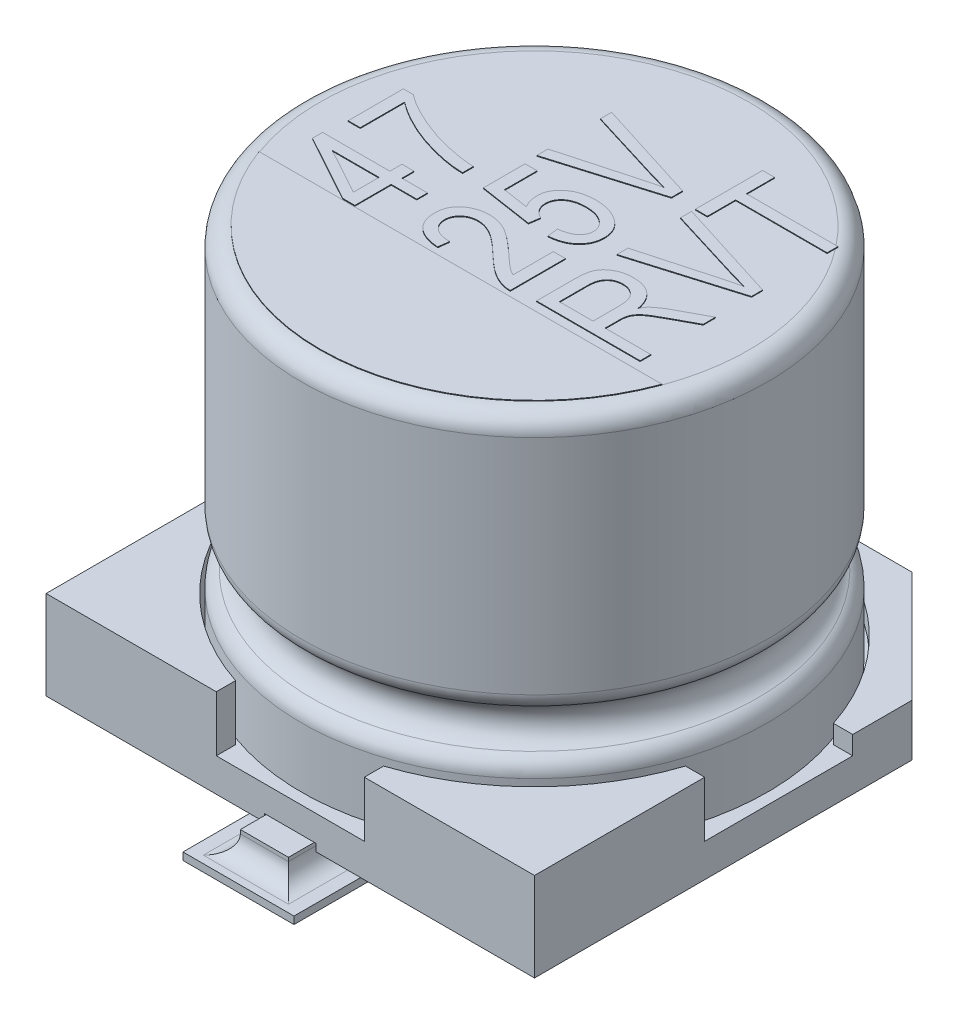
SolidWorks part; units mm, degrees
material "普通碳钢"
ref_plane "Front Plane" through (0, 0, 0) normal (0, 0, 1) x (1, 0, 0)
ref_plane "Top Plane" through (0, 0, 0) normal (0, 1, 0) x (1, 0, 0)
ref_plane "Right Plane" through (0, 0, 0) normal (1, 0, 0) x (0, 0, -1)
ref_plane "Plane1" through (0, 0.3, 0) normal (0, 1, 0) x (1, 0, 0)
sketch "Sketch1" plane through (0, 0.3, 0) normal (0, 1, 0) x (1, 0, 0)
  line L0 (-55, 0) -> (55, 0) construction
  line L1 (-3.3, -3.3) -> (3.3, -3.3)
  line L2 (-3.3, -3.3) -> (-3.3, 3.3)
  line L3 (-3.3, 3.3) -> (3.3, 3.3)
  line L4 (3.3, -3.3) -> (3.3, 3.3)
  line L5 (0, -55) -> (0, 55) construction
  dimension "D1" = 6.6
  dimension "D2" = 6.6
  dimension "D3" = 3.3
  dimension "D4" = 3.3
extrude "Boss-Extrude1" add sketch "Sketch1" along normal blind 1.2
sketch "Sketch2" plane through (0, 1.5, 0) normal (0, 1, 0) x (1, 0, 0)
  line L0 (-3.3, 1) -> (-3.0397, 1)
  line L1 (-3.3, 3.3) -> (-3.3, -3.3) construction
  line L2 (3.3, -3.3) -> (3.3, 3.3) construction
  line L3 (3.3, 1) -> (3.3, -1)
  line L4 (3.3, -1) -> (3.0397, -1)
  line L5 (-3.3, -1) -> (-3.3, 1)
  line L6 (3.3, 3.3) -> (-3.3, 3.3) construction
  line L7 (-1, 3.3) -> (1, 3.3)
  line L8 (-1, 3.3) -> (-1, 3.0397)
  line L9 (-1, -3.3) -> (1, -3.3)
  line L10 (1, 3.3) -> (1, 3.0397)
  line L11 (-3.3, -3.3) -> (3.3, -3.3) construction
  line L15 (-3.0397, -1) -> (-3.3, -1)
  line L16 (-1, -3.0397) -> (-1, -3.3)
  line L17 (1, -3.0397) -> (1, -3.3)
  line L19 (3.0397, 1) -> (3.3, 1)
  line L20 (-55, 0) -> (55, 0) construction
  line L22 (0, -55) -> (0, 55) construction
  arc A0 (3.0397, 1) -> (1, 3.0397) centre (0, 0) ccw
  arc A1 (-1, 3.0397) -> (-3.0397, 1) centre (0, 0) ccw
  arc A2 (-3.0397, -1) -> (-1, -3.0397) centre (0, 0) ccw
  arc A3 (1, -3.0397) -> (3.0397, -1) centre (0, 0) ccw
  dimension "D1" = 6.4
  dimension "D2" = 1
  dimension "D3" = 1
  dimension "D4" = 1
extrude "Cut-Extrude1" cut sketch "Sketch2" against normal blind 0.75
sketch "Sketch3" plane through (0, 0, 0) normal (1, 0, 0) x (0, 0, -1)
  line L0 (0, 55) -> (0, -55) construction
  line L1 (3.3, 1.5) -> (0, 1.5)
  line L2 (3.3, 1.5) -> (3.3, 1)
  line L3 (3.3, 1) -> (0, 1)
  line L4 (0, 1.5) -> (0, 1)
  dimension "D1" = 0.5
extrude "Cut-Extrude2" cut sketch "Sketch3" against normal through all and the other way through all
chamfer "Chamfer1" distance 1.5 angle 45 2 edges at (-3.3, 0.65, -3.3) (3.3, 0.65, -3.3)
sketch "Sketch4" plane through (0, 0, 0) normal (1, 0, 0) x (0, 0, -1)
  line L0 (0, 0) -> (0, 7.4696) construction
  line L1 (0, 55) -> (0, -55) construction
  line L2 (0, 0.75) -> (0, 5.8)
  line L3 (-1, 0.75) -> (1, 0.75) construction
  line L4 (0, 5.8) -> (-2.9, 5.8)
  line L5 (-3.15, 5.55) -> (-3.15, 2.5399)
  line L6 (-3.15, 1.5601) -> (-3.15, 0.75)
  line L7 (-3.15, 0.75) -> (0, 0.75)
  line L9 (55, 0) -> (-55, 0) construction
  arc A0 (-2.9, 5.8) -> (-3.15, 5.55) centre (-2.9, 5.55) ccw
  arc A1 (-3.0136, 2.3172) -> (-3.0136, 1.7828) centre (-3.15, 2.05) cw
  arc A2 (-3.0136, 1.7828) -> (-3.15, 1.5601) centre (-2.9, 1.5601) ccw
  arc A3 (-3.15, 2.5399) -> (-3.0136, 2.3172) centre (-2.9, 2.5399) ccw
  point P20 (-3.15, 1.75)
  dimension "D2" = 0.3
  dimension "D5" = 0.25
  dimension "D6" = 0.25
  dimension "D1" = 6.3
  dimension "D3" = 1
  dimension "D4" = 5.8
revolve "Revolve1" add sketch "Sketch4" angle 360 about L0
sketch "Sketch6" plane through (0, 0.3, 0) normal (0, -1, 0) x (1, 0, 0)
  line L0 (0, -55) -> (0, 55) construction
  line L1 (-0.325, -1.225) -> (-0.325, -3.65)
  line L2 (-0.325, -3.65) -> (0.325, -3.65)
  line L3 (0.325, -3.65) -> (0.325, -1.225)
  line L4 (-0.325, 1.225) -> (-0.325, 3.65)
  line L5 (-0.325, 3.65) -> (0.325, 3.65)
  line L6 (0.325, 3.65) -> (0.325, 1.225)
  line L7 (55, 0) -> (-55, 0) construction
  line L8 (-3.3, 3.3) -> (3.3, 3.3) construction
  line L9 (1.8, -3.3) -> (-1.8, -3.3) construction
  arc A0 (-0.325, 1.225) -> (0.325, 1.225) centre (0, 1.225) ccw
  arc A1 (0.325, -1.225) -> (-0.325, -1.225) centre (0, -1.225) ccw
  dimension "D1" = 0.65
  dimension "D2" = 2.45
  dimension "D3" = 1.225
  dimension "D4" = 0.35
  dimension "D5" = 0.35
sketch "Sketch7" plane through (0, 0.3, 0) normal (0, -1, 0) x (1, 0, 0)
  line L0 (-0.35, 3.3) -> (0.35, 3.3)
  line L1 (-3.3, 3.3) -> (3.3, 3.3) construction
  line L2 (0.35, 3.3) -> (0.4987, 1.2614)
  line L3 (-0.4987, 1.2614) -> (-0.35, 3.3)
  line L4 (-0.35, -3.3) -> (0.35, -3.3)
  line L5 (1.8, -3.3) -> (-1.8, -3.3) construction
  line L6 (-0.4987, -1.2614) -> (-0.35, -3.3)
  line L7 (0.4987, -1.2614) -> (0.35, -3.3)
  line L8 (0, -55) -> (0, 55) construction
  arc A0 (-0.4987, 1.2614) -> (0.4987, 1.2614) centre (0, 1.225) ccw
  arc A1 (0.4987, -1.2614) -> (-0.4987, -1.2614) centre (0, -1.225) ccw
  dimension "D3" = 1
  dimension "D1" = 0.7
  dimension "D2" = 0.35
extrude "Cut-Extrude3" cut sketch "Sketch7" against normal blind 0.1
extrude "Boss-Extrude4" add sketch "Sketch6" against normal blind 0.1 and the other way blind 0.3
sketch "Sketch8" plane through (0, 0.3, 0) normal (0, -1, 0) x (1, 0, 0)
  line L0 (0, -55) -> (0, 55) construction
  line L1 (-2, 2) -> (2, 2) construction
  line L2 (-2, 2) -> (-2, -2) construction
  line L3 (-2, -2) -> (2, -2) construction
  line L4 (2, 2) -> (2, -2) construction
  line L5 (55, 0) -> (-55, 0) construction
  circle A0 centre (-2, 2) radius 0.5
  circle A1 centre (2, 2) radius 0.5
  circle A2 centre (2, -2) radius 0.5
  circle A3 centre (-2, -2) radius 0.5
  dimension "D1" = 1
  dimension "D2" = 2
  dimension "D3" = 2
  dimension "D4" = 2
  dimension "D5" = 2
extrude "Boss-Extrude5" add sketch "Sketch8" along normal blind 0.3
sketch "Sketch9" plane through (0, 0, 0) normal (0, 1, 0) x (1, 0, 0)
  line L0 (-3.19, 0) -> (3.19, 0) construction
  line L1 (-0.75, 4) -> (0.75, 4)
  line L2 (-0.75, 4) -> (-0.75, 2)
  line L3 (-0.75, 2) -> (0.75, 2)
  line L4 (0.75, 4) -> (0.75, 2)
  line L5 (-0.75, -2) -> (0.75, -2)
  line L6 (-0.75, -2) -> (-0.75, -4)
  line L7 (-0.75, -4) -> (0.75, -4)
  line L8 (0.75, -2) -> (0.75, -4)
  line L9 (0, -3.19) -> (0, 3.19) construction
  dimension "D1" = 2
  dimension "D2" = 4
  dimension "D3" = 1.5
  dimension "D4" = 0.75
  dimension "D5" = 4
extrude "Boss-Extrude6" add sketch "Sketch9" along normal blind 0.1
fillet "Fillet1" radius 0.25 6 edges at (-0.325, 0.1, -2.825) (0, 0.1, -3.65) (0.325, 0.1, -2.825) (-0.325, 0.1, 2.825) (0.325, 0.1, 2.825) (0, 0.1, 3.65)
sketch "Sketch10" plane through (0, 5.8, 0) normal (0, 1, 0) x (1, 0, 0)
  line L0 (-2.7221, -1) -> (2.7221, -1)
  line L1 (-3.19, 0) -> (3.19, 0) construction
  line L2 (-1.1, -1) -> (-1.1, 2) construction
  line L3 (0, -3.19) -> (0, 3.19) construction
  line L4 (0.6, -1) -> (0.6, 2) construction
  line L6 (2.3, -1) -> (2.3, 2) construction
  circle A0 centre (0, 0) radius 2.9 construction
  arc A1 (-2.7221, -1) -> (2.7221, -1) centre (0, 0) ccw
  text T0 "47" font "Arial Narrow" height 1.4
  text T1 "25V" font "Arial Narrow" height 1.4
  text T2 "RVT" font "Arial Narrow" height 1.4
  dimension "D1" = 1
  dimension "D2" = 1.1
  dimension "D3" = 1.7
  dimension "D4" = 1.7
  dimension "D5" = 3
extrude "Boss-Extrude7" add sketch "Sketch10" along normal blind 0.01
